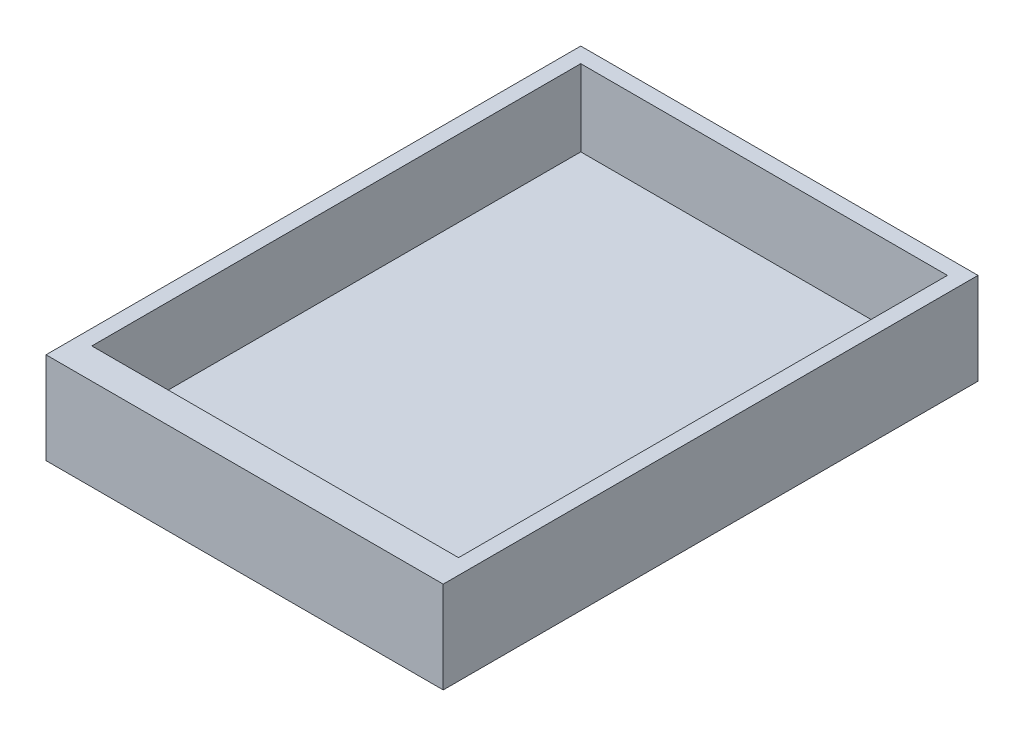
SolidWorks part; units mm, degrees
ref_plane "Front Plane" through (0, 0, 0) normal (0, 0, 1) x (1, 0, 0)
ref_plane "Top Plane" through (0, 0, 0) normal (0, 1, 0) x (1, 0, 0)
ref_plane "Right Plane" through (0, 0, 0) normal (1, 0, 0) x (0, 0, -1)
sketch "Sketch1" plane through (0, 0, 0) normal (0, 1, 0) x (1, 0, 0)
  line L1 (-41.275, -55.5625) -> (41.275, -55.5625)
  line L2 (-41.275, -55.5625) -> (-41.275, 55.5625)
  line L3 (-41.275, 55.5625) -> (41.275, 55.5625)
  line L4 (41.275, -55.5625) -> (41.275, 55.5625)
  line L5 (-41.275, -55.5625) -> (41.275, 55.5625) construction
  line L6 (-41.275, 55.5625) -> (41.275, -55.5625) construction
  point P0 (0, 0)
  dimension "D1" = 82.55
  dimension "D2" = 111.125
extrude "Boss-Extrude1" add sketch "Sketch1" along normal blind 19.05
sketch "Sketch14" plane through (0, 19.05, 0) normal (0, 1, 0) x (-1, 0, 0)
  line L0 (0, 0) -> (0, -1.5875) construction
  line L3 (38.1, 49.2125) -> (-38.1, 49.2125)
  line L4 (38.1, 49.2125) -> (38.1, -52.3875)
  line L5 (38.1, -52.3875) -> (-38.1, -52.3875)
  line L6 (-38.1, 49.2125) -> (-38.1, -52.3875)
  line L7 (38.1, 49.2125) -> (-38.1, -52.3875) construction
  line L8 (38.1, -52.3875) -> (-38.1, 49.2125) construction
  dimension "D1" = 1.5875
  dimension "D2" = 101.6
  dimension "D3" = 76.2
extrude "Cut-Extrude3" cut sketch "Sketch14" against normal offset from surface (15.875 mm away) 3.175 up to face at (0, 0, 0)
